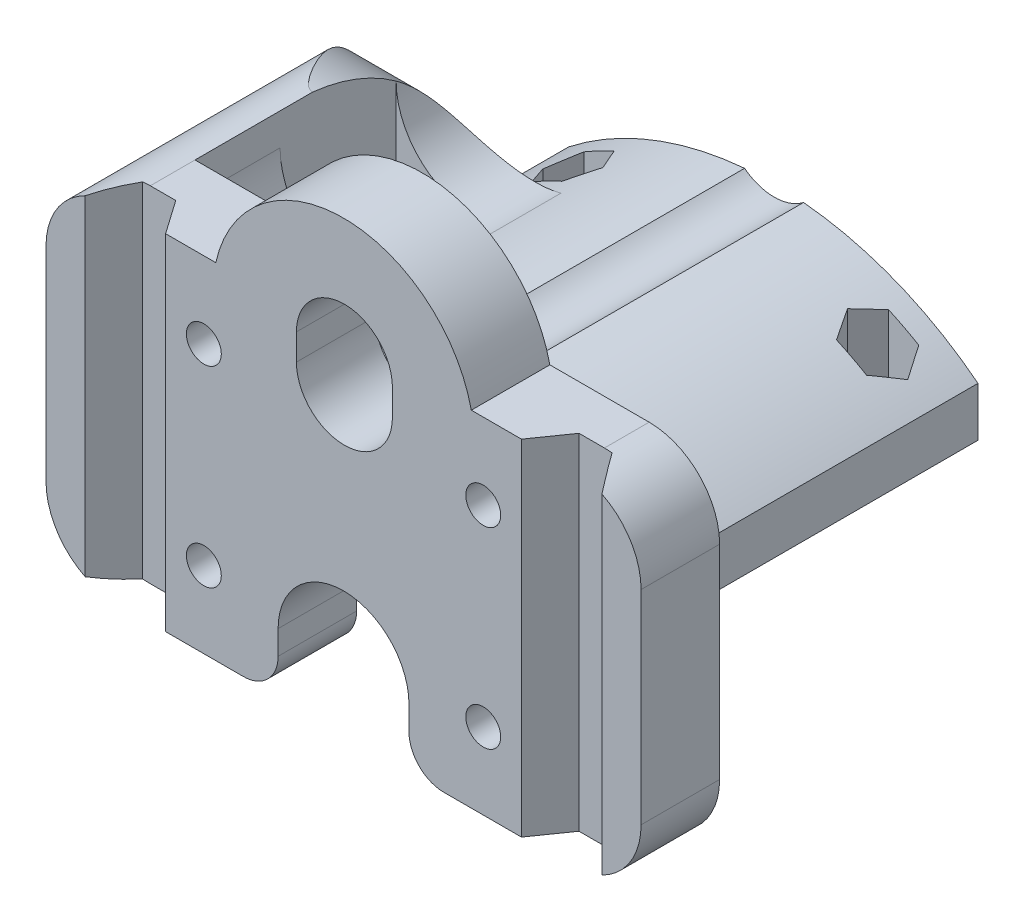
SolidWorks part; units mm, degrees
material "ABS"
ref_plane "Front Plane" through (0, 0, 0) normal (0, 0, 1) x (1, 0, 0)
ref_plane "Top Plane" through (0, 0, 0) normal (0, 1, 0) x (1, 0, 0)
ref_plane "Right Plane" through (0, 0, 0) normal (1, 0, 0) x (0, 0, -1)
sketch "Sketch1" plane through (0, 0, 0) normal (0, 0, 1) x (1, 0, 0)
  line L0 (0, 45.1417) -> (0, -45.2915) construction
  line L1 (-26.025, -19.75) -> (-11.5, -19.75)
  line L2 (-34.1, -11.675) -> (-34.1, 11.675)
  line L3 (-26.025, 19.75) -> (-14.6437, 19.75)
  line L4 (34.1, -11.675) -> (34.1, 11.675)
  line L5 (-34.1, -19.75) -> (34.1, 19.75) construction
  line L6 (-34.1, 19.75) -> (34.1, -19.75) construction
  line L7 (-7.5, -13) -> (-7.5, -15.75)
  line L8 (7.5, -13) -> (7.5, -15.75)
  line L9 (26.025, -19.75) -> (11.5, -19.75)
  line L10 (-42.1763, 0) -> (46.3672, 0) construction
  line L11 (-38.2382, 16.5) -> (49.0349, 16.5) construction
  line L12 (14.6437, 19.75) -> (26.025, 19.75)
  arc A0 (7.5, -13) -> (-7.5, -13) centre (0, -13) ccw
  arc A1 (-34.1, 11.675) -> (-26.025, 19.75) centre (-26.025, 11.675) cw
  arc A2 (-26.025, -19.75) -> (-34.1, -11.675) centre (-26.025, -11.675) cw
  arc A3 (26.025, 19.75) -> (34.1, 11.675) centre (26.025, 11.675) cw
  arc A4 (34.1, -11.675) -> (26.025, -19.75) centre (26.025, -11.675) cw
  arc A5 (-7.5, -15.75) -> (-11.5, -19.75) centre (-11.5, -15.75) cw
  arc A6 (7.5, -15.75) -> (11.5, -19.75) centre (11.5, -15.75) ccw
  circle A7 centre (-16.01, 11) radius 2
  circle A8 centre (16.01, 11) radius 2
  circle A9 centre (16.01, -11) radius 2
  circle A10 centre (-16.01, -11) radius 2
  arc A11 (14.6437, 19.75) -> (-14.6437, 19.75) centre (0, 16.5) ccw
  arc A12 (14.0162, 11.1571) -> (14.3406, 12.1014) centre (0, 16.5) ccw
  arc A14 (-14.3406, 12.1014) -> (-14.0162, 11.1571) centre (0, 16.5) ccw
  point P0 (0, 0)
  point P30 (7.5, -19.75)
  point P42 (0, 16.5)
  dimension "D4" = 15
  dimension "D5" = 8.075
  dimension "D6" = 8.075
  dimension "D7" = 8.075
  dimension "D8" = 8.075
  dimension "D9" = 4
  dimension "D10" = 4
  dimension "D11" = 4
  dimension "D15" = 30
  dimension "D1" = 68.2
  dimension "D2" = 39.5
  dimension "D3" = 6.75
  dimension "D12" = 18.09
  dimension "D13" = 8.75
  dimension "D14" = 3.25
extrude "Boss-Extrude1" add sketch "Sketch1" against normal blind 49.25 contours L12 A11 L3 A1 L2 A2 L1 A5 L7 A0 L8 A6 L9 A4 L4 A3 A10 A9 A7 A8
sketch "Sketch2" plane through (0, 0, -49.25) normal (0, 0, -1) x (-1, 0, 0)
  line L0 (0, 41.3246) -> (0, -40.105) construction
  line L1 (-23.4625, -3.45) -> (23.4625, -3.45)
  line L2 (-26.025, -19.75) -> (-11.5, -19.75) construction
  line L3 (-23.4625, -3.45) -> (-23.4625, 2.2)
  line L4 (23.4625, -3.45) -> (23.4625, 2.2)
  arc A0 (23.4625, 2.2) -> (-23.4625, 2.2) centre (0, -27.6853) ccw
  point P6 (0, -3.45)
  circle M5 centre (16.01, -11) radius 2
  circle M6 centre (-16.01, -11) radius 2
  circle M7 centre (16.01, 11) radius 2
  circle M8 centre (-16.01, 11) radius 2
  line M9 (-14.6437, 19.75) -> (-26.025, 19.75)
  arc M10 (-26.025, 19.75) -> (-34.1, 11.675) centre (-26.025, 11.675) ccw
  line M11 (-34.1, 11.675) -> (-34.1, -11.675)
  arc M12 (-34.1, -11.675) -> (-26.025, -19.75) centre (-26.025, -11.675) ccw
  line M13 (-26.025, -19.75) -> (-11.5, -19.75)
  arc M14 (-11.5, -19.75) -> (-7.5, -15.75) centre (-11.5, -15.75) ccw
  line M15 (-7.5, -15.75) -> (-7.5, -13)
  arc M16 (-7.5, -13) -> (7.5, -13) centre (0, -13) cw
  line M17 (7.5, -13) -> (7.5, -15.75)
  arc M18 (7.5, -15.75) -> (11.5, -19.75) centre (11.5, -15.75) ccw
  line M19 (11.5, -19.75) -> (26.025, -19.75)
  arc M20 (26.025, -19.75) -> (34.1, -11.675) centre (26.025, -11.675) ccw
  line M21 (34.1, -11.675) -> (34.1, 11.675)
  arc M22 (34.1, 11.675) -> (26.025, 19.75) centre (26.025, 11.675) ccw
  line M23 (26.025, 19.75) -> (14.6437, 19.75)
  arc M24 (14.6437, 19.75) -> (-14.6437, 19.75) centre (0, 16.5) ccw
  dimension "D4" = 37.995
  dimension "D1" = 16.3
  dimension "D2" = 46.925
  dimension "D3" = 5.65
extrude "Cut-Extrude1" cut sketch "Sketch2" against normal blind 40.25 contours L0 A0 L4 L1 M24 M16 M17 M18 M19 M20 M21 M22 M23 M5 M7 | L0 L1 L3 A0 M24 M9 M10 M11 M12 M13 M14 M15 M16 M6 M8
sketch "Sketch3" plane through (0, 0, -49.25) normal (0, 0, -1) x (-1, 0, 0)
  line L0 (5.4, 17.5) -> (5.4, 14.5)
  line L1 (-5.6, 17.5) -> (-5.6, 14.5)
  line L2 (-34.1, 11.675) -> (-34.1, -11.675) construction
  line L3 (-26.025, -19.75) -> (-11.5, -19.75) construction
  arc A0 (5.4, 17.5) -> (-5.6, 17.5) centre (-0.1, 17.5) ccw
  arc A1 (-5.6, 14.5) -> (5.4, 14.5) centre (-0.1, 14.5) ccw
  dimension "D5" = 5.5
  dimension "D6" = 5.5
  dimension "D1" = 34
  dimension "D2" = 37.25
  dimension "D3" = 3
  dimension "D7" = 34
  dimension "D8" = 34.25
extrude "Cut-Extrude2" cut sketch "Sketch3" against normal through all
sketch "Sketch4" plane through (0, 0, -9) normal (0, 0, -1) x (-1, 0, 0)
  line L0 (26.025, 19.75) -> (26.025, 16.08)
  line L1 (34.1, 11.675) -> (34.1, -11.675)
  line L2 (23.4625, -3.45) -> (26.6625, -3.45)
  line L3 (26.6625, -3.45) -> (26.6625, -19.7248)
  line L5 (23.4625, -3.45) -> (23.4625, 2.2)
  arc A0 (26.025, 16.08) -> (13.7928, 7.7178) centre (17.0506, 16.08) cw
  arc A1 (23.4625, 2.2) -> (3.2878, 10.1672) centre (0, -27.6853) ccw construction
  arc A2 (23.4625, 2.2) -> (3.2878, 10.1672) centre (0, -27.6853) ccw construction
  arc A3 (26.025, 19.75) -> (34.1, 11.675) centre (26.025, 11.675) cw
  arc A4 (34.1, -11.675) -> (26.025, -19.75) centre (26.025, -11.675) cw
  arc A5 (13.7928, 7.7178) -> (23.4625, 2.2) centre (0, -27.6853) cw
  arc A6 (26.025, -19.75) -> (34.1, -11.675) centre (26.025, -11.675) ccw construction
  arc M4 (3.2878, 10.1672) -> (23.4625, 2.2) centre (0, -27.6853) cw
  line M5 (23.4625, 2.2) -> (23.4625, -3.45)
  arc M27 (26.025, -19.75) -> (34.1, -11.675) centre (26.025, -11.675) ccw
  line M28 (34.1, -11.675) -> (34.1, 11.675)
  arc M29 (34.1, 11.675) -> (26.025, 19.75) centre (26.025, 11.675) ccw
  dimension "D1" = 3.67
  dimension "D3" = 3.2
extrude "Boss-Extrude2" add sketch "Sketch4" along normal blind 30.5 contours L0 A0 L2 L3 M4 M5 M27 M28 M29
sketch "Sketch5" plane through (-34.1, 0, 0) normal (-1, 0, 0) x (0, 0, 1)
  line L0 (-39.5, 19.75) -> (-9, 19.75) construction
  line L1 (-39.5, -11.675) -> (-39.5, 11.675) construction
  line L2 (0, 19.75) -> (-22.5, 19.75)
  line L3 (-22.5, 19.75) -> (-39.5, 19.75)
  line L4 (-39.5, 19.75) -> (-39.5, 5.4752)
  line L5 (-39.5, -19.7248) -> (-9, -19.7248) construction
  arc A0 (-22.5, 19.75) -> (-39.5, 5.4752) centre (-20.3012, -0.1288) ccw
  line M2 (0, 11.675) -> (-39.5, 11.675)
  line M3 (-39.5, 11.675) -> (-39.5, -11.675)
  dimension "D1" = 20
  dimension "D2" = 22.5
  dimension "D3" = 25.2
extrude "Cut-Extrude3" cut sketch "Sketch5" against normal up to next contours A0 L3 L4 M2 | A0 M2 M3
sketch "Sketch6" plane through (0, 0, -49.25) normal (0, 0, -1) x (-1, 0, 0)
  line L0 (-23.4625, 2.2) -> (-23.4625, -3.45)
  line L1 (-23.4625, -3.45) -> (23.4625, -3.45)
  line L2 (23.4625, -3.45) -> (23.4625, 2.2)
  arc A0 (-23.4625, 2.2) -> (-3.4672, 10.1512) centre (0, -27.6853) cw
  arc A1 (23.4625, 2.2) -> (3.2878, 10.1672) centre (0, -27.6853) ccw
  arc A2 (-3.4672, 10.1512) -> (3.2878, 10.1672) centre (-0.1, 14.5) ccw
  dimension "D1" = 37.995
  dimension "D2" = 37.995
  dimension "D3" = 5.5
extrude "Boss-Extrude3" add sketch "Sketch6" against normal blind 19.5
sketch "Sketch7" plane through (-34.1, 0, 0) normal (-1, 0, 0) x (0, 0, 1)
  line L0 (-39.5, -19.7248) -> (-9, -19.7248) construction
  line L1 (-39.5, -11.675) -> (-39.5, 5.4752) construction
  line L2 (-39.5, -3.45) -> (-49.25, -3.45) construction
  line L3 (0, 11.675) -> (0, -39.662) construction
  line L4 (-39.5, -5.75) -> (-39.5, -19.7248)
  line L5 (-39.5, -19.7248) -> (-23.95, -19.7248)
  line L6 (-23.95, -19.7248) -> (-10.5898, -19.7248) construction
  arc A0 (-23.95, -19.7248) -> (-39.5, -5.75) centre (-20.3278, -0.0555) cw
  dimension "D1" = 20
  dimension "D2" = 2.3
  dimension "D3" = 23.95
extrude "Cut-Extrude4" cut sketch "Sketch7" against normal blind 19.5
sketch "Sketch8" plane through (0, 19.75, 0) normal (0, 1, 0) x (1, 0, 0)
  line L0 (-26.025, 32.05) -> (-17.075, 32.05)
  line L1 (-26.025, 22.5) -> (-26.025, 32.0176) construction
  line L2 (-17.075, 32.05) -> (-17.075, 18.75)
  line L3 (-17.075, 18.75) -> (-26.025, 18.75)
  line L4 (-26.025, 22.5) -> (-26.025, 9) construction
  line L5 (-26.025, 18.75) -> (-26.025, 32.05)
  line L6 (-17.075, 20.6355) -> (-18.9605, 18.75)
  line L7 (-26.025, 0) -> (-14.6437, 0) construction
  dimension "D1" = 13.3
  dimension "D2" = 8.95
  dimension "D3" = 2.6665
  dimension "D4" = 45
  dimension "D5" = 18.75
extrude "Cut-Extrude5" cut sketch "Sketch8" against normal blind 40.5 contours L6 L2 L0 L5 L3
sketch "Sketch9" plane through (0, 0, -9) normal (0, 0, -1) x (-1, 0, 0)
  circle A0 centre (-16.01, 11) radius 4.05
  circle A1 centre (16.01, 11) radius 4.05
  circle A2 centre (-16.01, -11) radius 4.05
  circle A3 centre (16.01, -11) radius 4.05
  dimension "D1" = 8.1
extrude "Cut-Extrude6" cut sketch "Sketch9" against normal blind 2.4
sketch "Sketch10" plane through (0, 19.75, 0) normal (0, 1, 0) x (1, 0, 0)
  line L0 (20.3917, 0) -> (23.1071, 3.878)
  line L1 (14.6437, 0) -> (26.025, 0) construction
  line L2 (23.1071, 3.878) -> (26.8971, 3.878)
  line L3 (26.8971, 3.878) -> (29.6125, 0)
  line L4 (26.025, 0) -> (34.1, 0) construction
  line L5 (29.6125, 0) -> (20.3917, 0)
  line L6 (-20.3916, 0) -> (-23.107, 3.878)
  line L7 (-26.025, 0) -> (-14.6437, 0) construction
  line L8 (-23.107, 3.878) -> (-26.897, 3.878)
  line L9 (-26.897, 3.878) -> (-29.6124, 0)
  line L10 (-34.1, 0) -> (-26.025, 0) construction
  line L11 (-29.6124, 0) -> (-20.3916, 0)
  dimension "D1" = 125
  dimension "D2" = 125
  dimension "D3" = 125
  dimension "D4" = 125
  dimension "D5" = 3.79
  dimension "D6" = 3.79
  dimension "D7" = 5.748
  dimension "D8" = 4.7342
  dimension "D9" = 4.7342
  dimension "D10" = 5.7479
extrude "Cut-Extrude7" cut sketch "Sketch10" against normal up to next
sketch "Sketch11" plane through (-34.1, 0, 0) normal (-1, 0, 0) x (0, 0, 1)
  line L0 (0, -11.675) -> (0, 11.675) construction
  line L1 (-22.5, 19.75) -> (-9, 19.75) construction
  circle A0 centre (-25, 3.9) radius 4.5
  dimension "D1" = 9
  dimension "D2" = 25
  dimension "D3" = 15.85
extrude "Cut-Extrude8" cut sketch "Sketch11" against normal up to next
sketch "Sketch12" plane through (0, -3.45, 0) normal (0, -1, 0) x (1, 0, 0)
  line L0 (23.4625, -49.25) -> (-23.4625, -49.25) construction
  line L1 (23.4625, -9) -> (23.4625, -49.25) construction
  line L2 (0, 23.4027) -> (0, -63.2721) construction
  line L3 (-23.4625, -39.5) -> (-23.4625, -49.25) construction
  circle A0 centre (-17.4625, -15) radius 1.8
  circle A1 centre (-17.4625, -43.75) radius 1.8
  circle A2 centre (17.4625, -15) radius 1.8
  circle A3 centre (17.4625, -43.75) radius 1.8
  dimension "D1" = 3.6
  dimension "D2" = 5.5
  dimension "D3" = 6
  dimension "D4" = 28.75
extrude "Cut-Extrude9" cut sketch "Sketch12" against normal up to next
ref_plane "Plane1" through (0, -1.1004, 0) normal (0, -1, 0) x (-1, 0, 0)
sketch "Sketch13" plane through (0, -1.1004, 0) normal (0, -1, 0) x (-1, 0, 0)
  line L0 (-23.4625, 49.25) -> (23.4625, 49.25) construction
  line L1 (-15.7374, 46.7379) -> (-19.1876, 46.7379)
  line L2 (-19.1876, 46.7379) -> (-20.9126, 43.75)
  line L3 (-20.9126, 43.75) -> (-19.1876, 40.7621)
  line L4 (-19.1876, 40.7621) -> (-15.7374, 40.7621)
  line L5 (-15.7374, 40.7621) -> (-14.0123, 43.75)
  line L6 (-14.0123, 43.75) -> (-15.7374, 46.7379)
  line L7 (-15.7374, 17.9879) -> (-19.1876, 17.9879)
  line L8 (-19.1876, 17.9879) -> (-20.9126, 15)
  line L9 (-20.9126, 15) -> (-19.1876, 12.0121)
  line L10 (-19.1876, 12.0121) -> (-15.7374, 12.0121)
  line L11 (-15.7374, 12.0121) -> (-14.0123, 15)
  line L12 (-14.0123, 15) -> (-15.7374, 17.9879)
  line L13 (19.1876, 17.9879) -> (15.7374, 17.9879)
  line L14 (15.7374, 17.9879) -> (14.0123, 15)
  line L15 (14.0123, 15) -> (15.7374, 12.0121)
  line L16 (15.7374, 12.0121) -> (19.1876, 12.0121)
  line L17 (19.1876, 12.0121) -> (20.9126, 15)
  line L18 (20.9126, 15) -> (19.1876, 17.9879)
  line L19 (15.7374, 40.7621) -> (19.1876, 40.7621)
  line L20 (19.1876, 40.7621) -> (20.9126, 43.75)
  line L21 (20.9126, 43.75) -> (19.1876, 46.7379)
  line L22 (19.1876, 46.7379) -> (15.7374, 46.7379)
  line L23 (15.7374, 46.7379) -> (14.0123, 43.75)
  line L24 (14.0123, 43.75) -> (15.7374, 40.7621)
  circle A0 centre (-17.4625, 43.75) radius 2.9879 construction
  circle A1 centre (-17.4625, 15) radius 2.9879 construction
  circle A2 centre (17.4625, 15) radius 2.9879 construction
  circle A3 centre (17.4625, 43.75) radius 2.9879 construction
  dimension "D1" = 3.4501
extrude "Cut-Extrude10" cut sketch "Sketch13" against normal up to next
